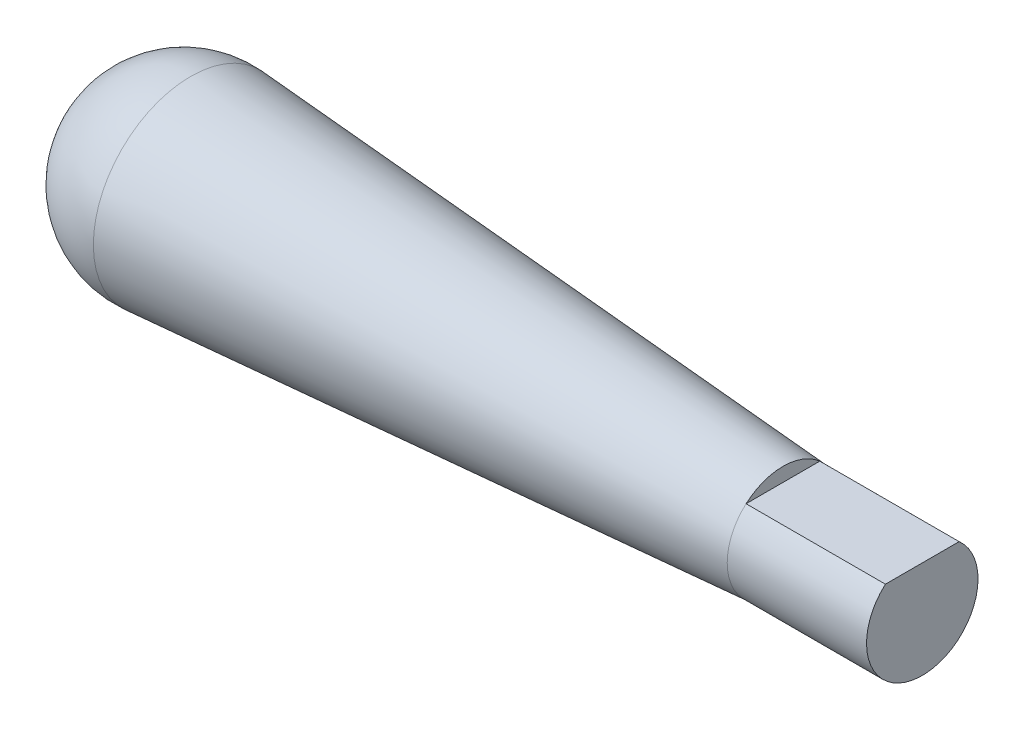
SolidWorks part; units mm, degrees
ref_plane "Ön Düzlem" through (0, 0, 0) normal (0, 0, 1) x (1, 0, 0)
ref_plane "Üst Düzlem" through (0, 0, 0) normal (0, 1, 0) x (1, 0, 0)
ref_plane "Sağ Düzlem" through (0, 0, 0) normal (1, 0, 0) x (0, 0, -1)
sketch "Çizim1" plane through (0, 0, 0) normal (0, 0, 1) x (1, 0, 0)
  line L0 (0, 0) -> (60, 0)
  line L1 (60, 0) -> (60, 4)
  line L2 (60, 4) -> (50, 4)
  line L3 (50, 4) -> (7.49, 6.9828)
  arc A0 (7.49, 6.9828) -> (0, 0) centre (7, 0) ccw
  dimension "D4" = 7
  dimension "D1" = 60
  dimension "D2" = 4
  dimension "D3" = 10
revolve "Döndür1" add sketch "Çizim1" angle 360 about L0
sketch "Çizim3" plane through (60, 0, 0) normal (1, 0, 0) x (0, 0, -1)
  line L1 (-8.5978, 5.6603) -> (8.6942, 5.6603)
  line L2 (-8.5978, 5.6603) -> (-8.5978, 3)
  line L3 (-8.5978, 3) -> (8.6942, 3)
  line L4 (8.6942, 5.6603) -> (8.6942, 3)
  dimension "D1" = 3
extrude "Kes-Ekstrüzyon1" cut sketch "Çizim3" against normal blind 10
